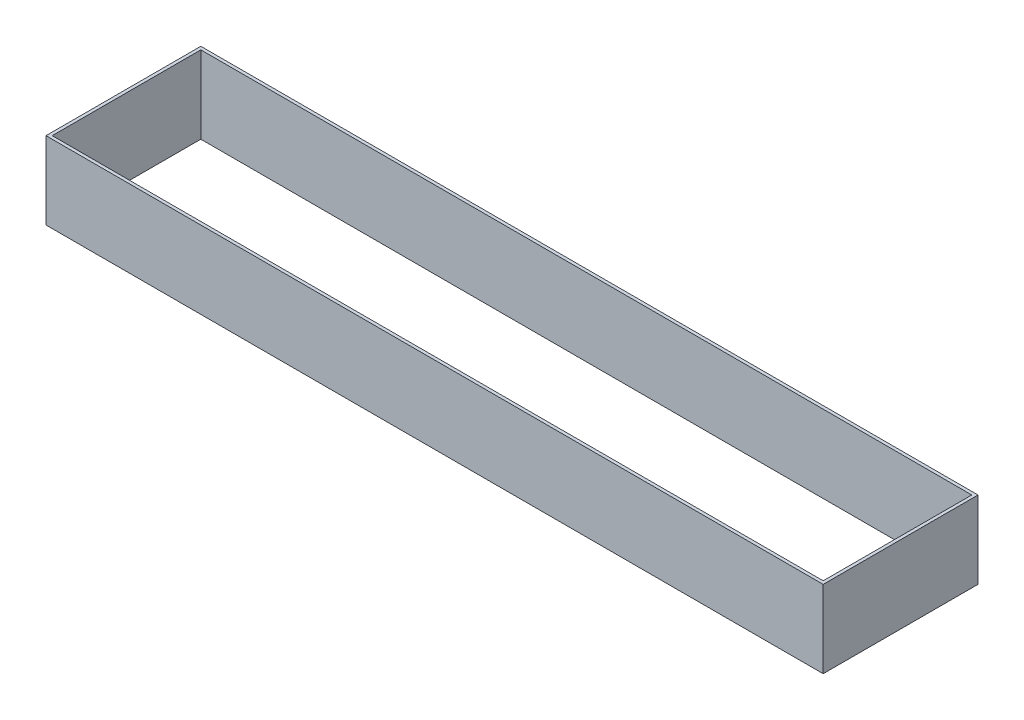
SolidWorks part; units mm, degrees
ref_plane "Front Plane" through (0, 0, 0) normal (0, 0, 1) x (1, 0, 0)
ref_plane "Top Plane" through (0, 0, 0) normal (0, 1, 0) x (1, 0, 0)
ref_plane "Right Plane" through (0, 0, 0) normal (1, 0, 0) x (0, 0, -1)
sketch "Sketch1" plane through (0, 0, 0) normal (0, 1, 0) x (1, 0, 0)
  line L0 (0.4, 19.6) -> (100, 19.6)
  line L1 (0, 0) -> (100.4, 0)
  line L2 (0, 0) -> (0, 20)
  line L3 (0, 20) -> (100.4, 20)
  line L4 (100.4, 0) -> (100.4, 20)
  line L5 (100, 0.4) -> (100, 19.6)
  line L6 (0.4, 0.4) -> (100, 0.4)
  line L7 (0.4, 0.4) -> (0.4, 19.6)
  point P11 (149.7753, 20)
  dimension "D1" = 20
  dimension "D2" = 100
  dimension "D3" = 0.4
extrude "Boss-Extrude1" add sketch "Sketch1" along normal blind 10
